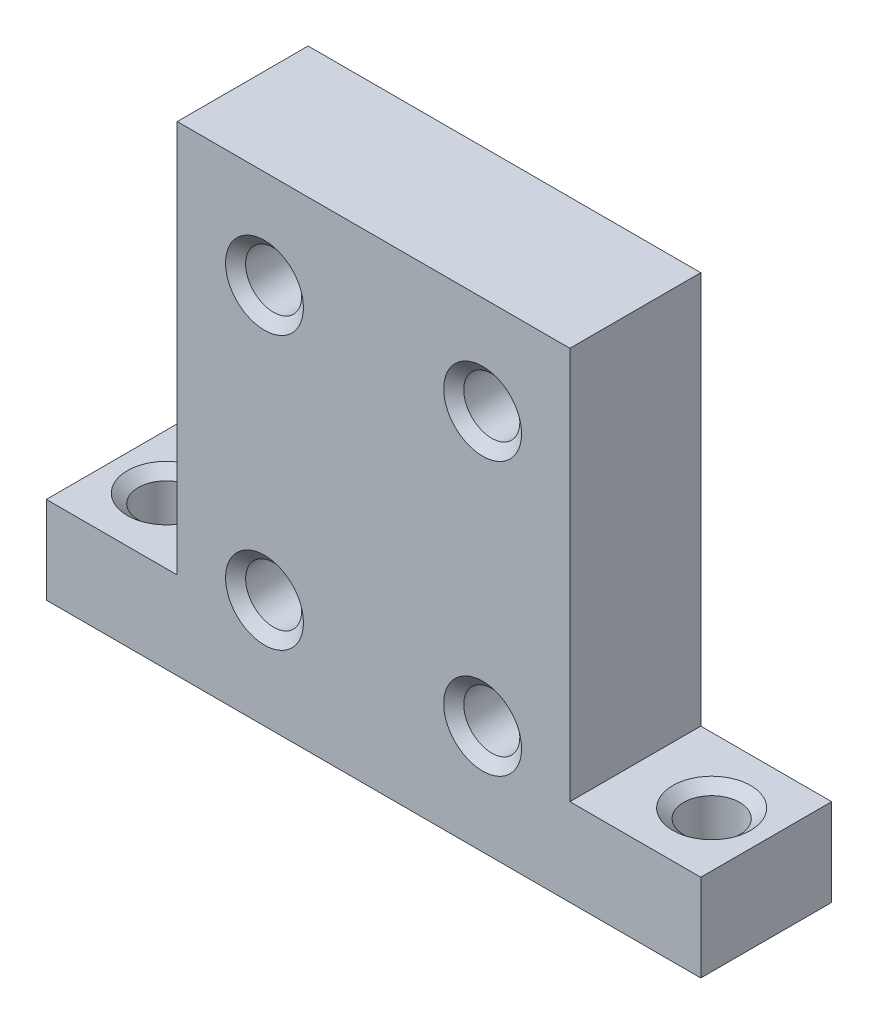
SolidWorks part; units mm, degrees
ref_plane "Front Plane" through (0, 0, 0) normal (0, 0, 1) x (1, 0, 0)
ref_plane "Top Plane" through (0, 0, 0) normal (0, 1, 0) x (1, 0, 0)
ref_plane "Right Plane" through (0, 0, 0) normal (1, 0, 0) x (0, 0, -1)
sketch "Sketch1" plane through (0, 0, 0) normal (0, 1, 0) x (1, 0, 0)
  line L1 (0, 0) -> (-38.1, 0)
  line L2 (0, 0) -> (0, 7.62)
  line L3 (0, 7.62) -> (-38.1, 7.62)
  line L4 (-38.1, 0) -> (-38.1, 7.62)
  dimension "D1" = 38.1
  dimension "D2" = 7.62
extrude "Boss-Extrude1" add sketch "Sketch1" along normal blind 5.08
sketch "Sketch2" plane through (0, 5.08, 0) normal (0, 1, 0) x (1, 0, 0)
  line L0 (0, 7.62) -> (-38.1, 7.62) construction
  line L1 (-30.48, 7.62) -> (-7.62, 7.62)
  line L2 (-30.48, 7.62) -> (-30.48, 0)
  line L3 (-30.48, 0) -> (-7.62, 0)
  line L4 (-7.62, 7.62) -> (-7.62, 0)
  line L5 (-38.1, 0) -> (0, 0) construction
  line L6 (0, 0) -> (0, 7.62) construction
  line L7 (-38.1, 7.62) -> (-38.1, 0) construction
  dimension "D1" = 7.62
  dimension "D2" = 7.62
extrude "Boss-Extrude2" add sketch "Sketch2" along normal blind 22.86
sketch "Sketch3" plane through (0, 0, 0) normal (0, 0, 1) x (1, 0, 0)
  line L0 (-19.05, 27.94) -> (-19.05, 0) construction
  line L1 (-30.48, 27.94) -> (-7.62, 27.94) construction
  line L2 (-38.1, 0) -> (0, 0) construction
hole_wizard "#4 Clearance Hole1" positions "3DSketch1" profile "Sketch4" hole size "#4" standard "ANSI Inch" end condition through all
sketch3d "3DSketch1"
  line L0 (-38.1, 0, 0) -> (0, 0, 0) construction
  line L1 (-19.05, 27.94, 0) -> (-19.05, 0, 0) construction
  point P0 (-25.4, 6.35, 0)
  point P2 (-25.4, 22.225, 0)
  point P4 (-12.7, 22.225, 0)
  point P6 (-12.7, 6.35, 0)
  dimension "D1" = 6.35
  dimension "D2" = 6.35
  dimension "D3" = 6.35
  dimension "D4" = 6.35
  dimension "D5" = 15.875
  dimension "D6" = 6.35
  dimension "D7" = 15.875
  dimension "D8" = 6.35
sketch "Sketch4" plane through (-25.4, 6.35, 0) normal (1, 0, 0) x (0, -1, 0)
  line L0 (0, 0) -> (0, 7.62)
  line L1 (0, 7.62) -> (1.6319, 7.62)
  line L2 (1.6319, 7.62) -> (1.6319, 0.5328)
  line L3 (1.6319, 0.5328) -> (2.267, 0)
  line L5 (2.267, 0) -> (0, 0)
  line L6 (-1.632, 0.5328) -> (-2.267, 0) construction
  line L11 (0, -6.35) -> (0, 107.95) construction
  dimension "Thru Hole Dia." = 3.2639
  dimension "Thru Hole Depth" = 7.62
  dimension "Near C'Sink Dia." = 4.5339
  dimension "Near C'Sink Angle" = 100
hole_wizard "#4 Clearance Hole2" positions "Sketch5" profile "Sketch6" hole size "#4" standard "ANSI Inch" end condition through all
sketch "Sketch5" plane through (0, 5.08, 0) normal (0, 1, 0) x (1, 0, 0)
  line L0 (-38.1, 0) -> (-30.48, 0) construction
  line L1 (-38.1, 7.62) -> (-38.1, 0) construction
  line L2 (-7.62, 0) -> (0, 0) construction
  line L3 (0, 0) -> (0, 7.62) construction
  point P0 (-34.925, 3.81)
  point P2 (-3.175, 3.81)
  dimension "D1" = 3.81
  dimension "D2" = 3.175
  dimension "D3" = 3.81
  dimension "D4" = 3.175
sketch "Sketch6" plane through (-34.925, 5.08, -3.81) normal (1, 0, 0) x (0, 0, 1)
  line L0 (0, 0) -> (0, 5.08)
  line L1 (0, 5.08) -> (1.6319, 5.08)
  line L2 (1.6319, 5.08) -> (1.6319, 0.5328)
  line L3 (1.6319, 0.5328) -> (2.267, 0)
  line L5 (2.267, 0) -> (0, 0)
  line L6 (-1.6319, 0.5328) -> (-2.267, 0) construction
  line L11 (0, -6.35) -> (0, 107.95) construction
  dimension "Thru Hole Dia." = 3.2639
  dimension "Thru Hole Depth" = 5.08
  dimension "Near C'Sink Dia." = 4.5339
  dimension "Near C'Sink Angle" = 100
